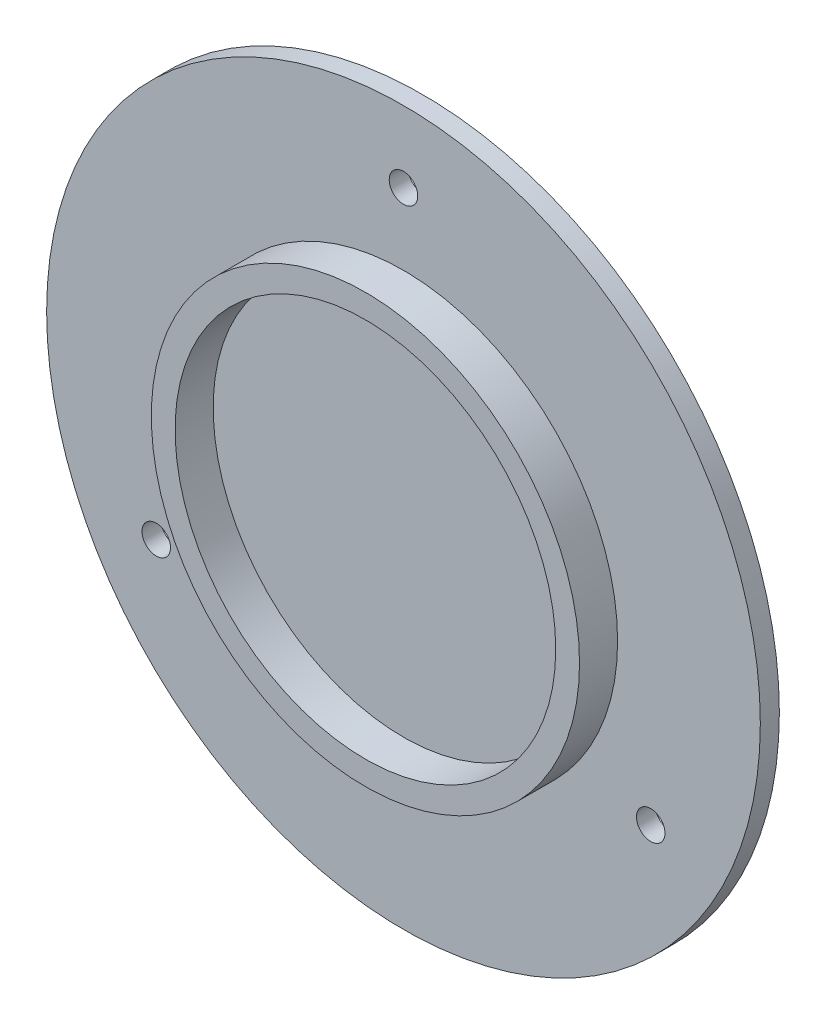
SolidWorks part; units mm, degrees
ref_plane "Front Plane" through (0, 0, 0) normal (0, 0, 1) x (1, 0, 0)
ref_plane "Top Plane" through (0, 0, 0) normal (0, 1, 0) x (1, 0, 0)
ref_plane "Right Plane" through (0, 0, 0) normal (1, 0, 0) x (0, 0, -1)
sketch "Sketch1" plane through (0, 0, 0) normal (0, 0, 1) x (1, 0, 0)
  circle A0 centre (0, 0) radius 75
extrude "Boss-Extrude1" add sketch "Sketch1" along normal blind 4
sketch "Sketch2" plane through (0, 0, 4) normal (0, 0, 1) x (1, 0, 0)
  circle A0 centre (0, 0) radius 45
  circle A1 centre (0, 0) radius 40
extrude "Boss-Extrude2" add sketch "Sketch2" along normal blind 8
sketch "Sketch4" plane through (0, 0, 0) normal (0, 0, -1) x (-1, 0, 0)
  circle A0 centre (0, 0) radius 60
  circle A1 centre (0, 60) radius 3
  circle A2 centre (51.9615, -30) radius 3
  circle A3 centre (-51.9615, -30) radius 3
  point P11 (0, 0)
  dimension "D1" = 3
extrude "Cut-Extrude1" cut sketch "Sketch4" against normal through all contours A2 | A1 | A3
